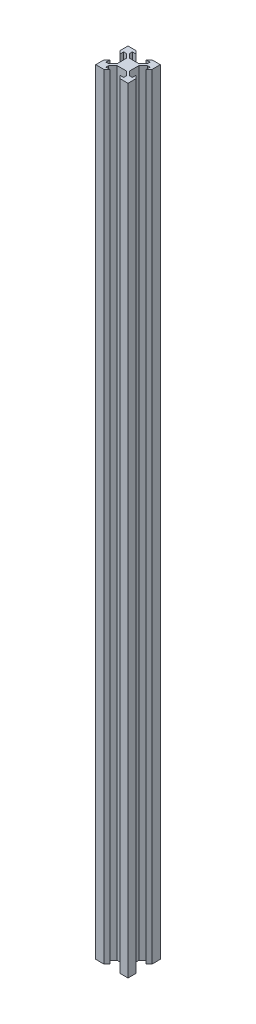
SolidWorks part; units mm, degrees
ref_plane "Front Plane" through (0, 0, 0) normal (0, 0, 1) x (1, 0, 0)
ref_plane "Top Plane" through (0, 0, 0) normal (0, 1, 0) x (1, 0, 0)
ref_plane "Right Plane" through (0, 0, 0) normal (1, 0, 0) x (0, 0, -1)
sketch "Sketch1" plane through (0, 0, 0) normal (0, 1, 0) x (1, 0, 0)
  line L0 (0, 93.8825) -> (0, -83.9719) construction
  line L1 (2.84, -3.9007) -> (-2.84, -3.9007)
  line L2 (3.9007, -2.84) -> (3.9007, 2.84)
  line L3 (2.84, 3.9007) -> (-2.84, 3.9007)
  line L4 (-3.9007, -2.84) -> (-3.9007, 2.84)
  line L7 (-194.997, 0) -> (154.5512, 0) construction
  line L8 (-2.84, -3.9007) -> (-5.4993, -6.56)
  line L9 (-5.4993, -6.56) -> (-5.4993, -8.2)
  line L10 (-5.4993, -8.2) -> (-3.1, -8.2)
  line L11 (-3.1, -8.2) -> (-4.9, -10)
  line L12 (-4.9, -10) -> (-10, -10)
  line L13 (-3.9007, -2.84) -> (-6.56, -5.4993)
  line L14 (-6.56, -5.4993) -> (-8.2, -5.4993)
  line L15 (-8.2, -5.4993) -> (-8.2, -3.1)
  line L16 (-8.2, -3.1) -> (-10, -4.9)
  line L17 (-10, -4.9) -> (-10, -10)
  line L18 (10, -4.9) -> (10, -10)
  line L19 (8.2, -3.1) -> (10, -4.9)
  line L20 (8.2, -5.4993) -> (8.2, -3.1)
  line L21 (6.56, -5.4993) -> (8.2, -5.4993)
  line L22 (3.9007, -2.84) -> (6.56, -5.4993)
  line L23 (4.9, -10) -> (10, -10)
  line L24 (3.1, -8.2) -> (4.9, -10)
  line L25 (5.4993, -8.2) -> (3.1, -8.2)
  line L26 (5.4993, -6.56) -> (5.4993, -8.2)
  line L27 (2.84, -3.9007) -> (5.4993, -6.56)
  line L28 (2.84, 3.9007) -> (5.4993, 6.56)
  line L29 (5.4993, 6.56) -> (5.4993, 8.2)
  line L30 (5.4993, 8.2) -> (3.1, 8.2)
  line L31 (3.1, 8.2) -> (4.9, 10)
  line L32 (4.9, 10) -> (10, 10)
  line L33 (3.9007, 2.84) -> (6.56, 5.4993)
  line L34 (6.56, 5.4993) -> (8.2, 5.4993)
  line L35 (8.2, 5.4993) -> (8.2, 3.1)
  line L36 (8.2, 3.1) -> (10, 4.9)
  line L37 (10, 4.9) -> (10, 10)
  line L38 (-10, 4.9) -> (-10, 10)
  line L39 (-8.2, 3.1) -> (-10, 4.9)
  line L40 (-8.2, 5.4993) -> (-8.2, 3.1)
  line L41 (-6.56, 5.4993) -> (-8.2, 5.4993)
  line L42 (-3.9007, 2.84) -> (-6.56, 5.4993)
  line L43 (-4.9, 10) -> (-10, 10)
  line L44 (-3.1, 8.2) -> (-4.9, 10)
  line L45 (-5.4993, 8.2) -> (-3.1, 8.2)
  line L46 (-5.4993, 6.56) -> (-5.4993, 8.2)
  line L47 (-2.84, 3.9007) -> (-5.4993, 6.56)
  point P0 (0, 0)
  point P4 (4.1697, 5.2303)
  dimension "D1" = 90
  dimension "D2" = 20
  dimension "D3" = 1.64
  dimension "D4" = 1.5
  dimension "D5" = 6.2
  dimension "D6" = 5.68
  dimension "D7" = 1.8
extrude "Boss-Extrude1" add sketch "Sketch1" along normal blind 480
